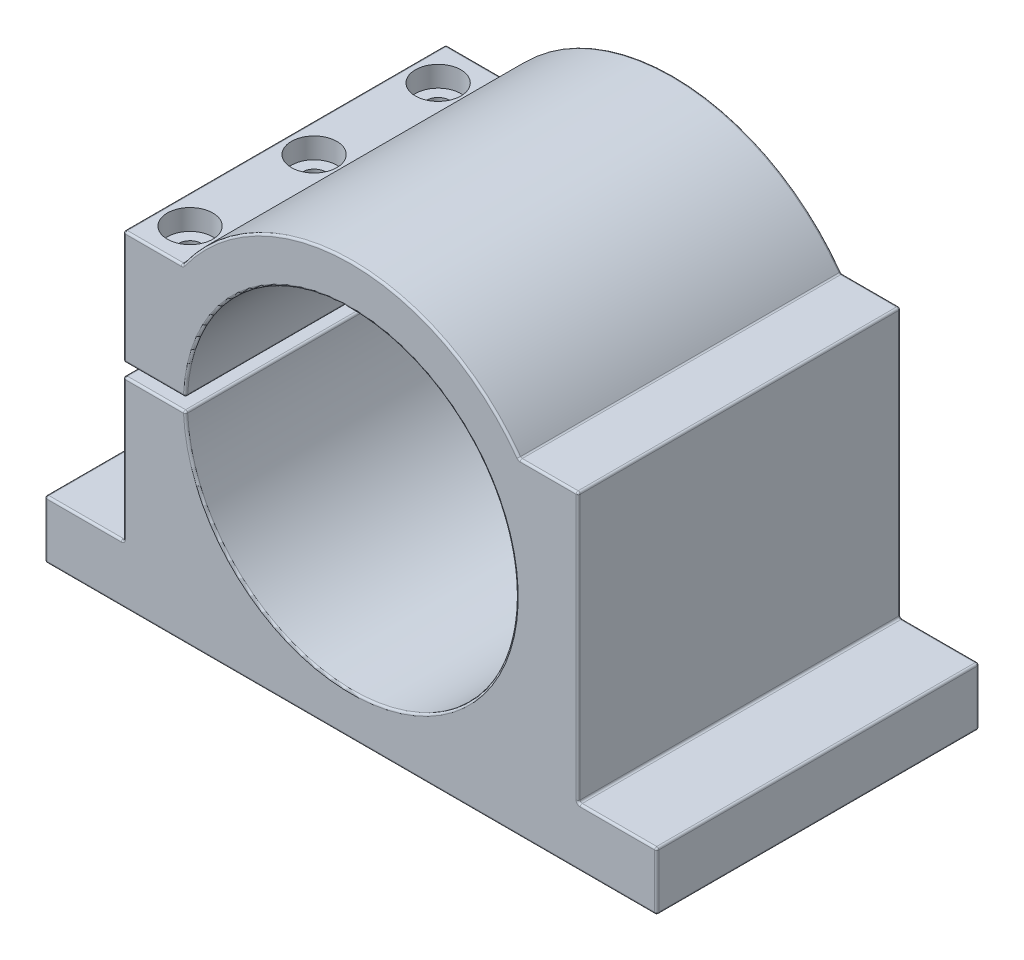
SolidWorks part; units mm, degrees
ref_plane "Спереди" through (0, 0, 0) normal (0, 0, 1) x (1, 0, 0)
ref_plane "Сверху" through (0, 0, 0) normal (0, 1, 0) x (1, 0, 0)
ref_plane "Справа" through (0, 0, 0) normal (1, 0, 0) x (0, 0, -1)
sketch "Эскиз1" plane through (0, 0, 0) normal (0, 0, 1) x (1, 0, 0)
  line L0 (0, 0) -> (0, -50) construction
  line L1 (74, -50) -> (-74, -50)
  line L2 (-74, -50) -> (-74, -36)
  line L3 (-74, -36) -> (-55, -36)
  line L4 (-55, -36) -> (-55, 29)
  line L5 (-55, 29) -> (-40.7308, 29)
  line L6 (0, 29) -> (-40.7308, 29) construction
  line L7 (-55, 1.5) -> (0, 1.5)
  line L8 (-55, 1.5) -> (-55, -1.5)
  line L9 (-55, -1.5) -> (0, -1.5)
  line L10 (0, 1.5) -> (0, -1.5)
  line L11 (0, 29) -> (0, 0) construction
  line L12 (0, -50) -> (0, 50) construction
  line L13 (55, 29) -> (40.7308, 29)
  line L14 (55, -36) -> (55, 29)
  line L15 (74, -36) -> (55, -36)
  line L16 (74, -50) -> (74, -36)
  circle A0 centre (0, 0) radius 40
  circle A2 centre (0, 0) radius 50
  point P13 (-27.55, 29)
  point P14 (0, 40)
  point P20 (0, 40)
  dimension "D1" = 80
  dimension "D2" = 3
  dimension "D3" = 50
  dimension "D4" = 14
  dimension "D5" = 148
  dimension "D6" = 19
  dimension "D7" = 65
  dimension "D8" = 10
extrude "Бобышка-Вытянуть1" add sketch "Эскиз1" along normal mid plane 78 contours A2 L1 L16 L15 L14 L13 | A2 L7 A0 L9 | A2 L9 L4 L3 L2 L1 | A2 L5 L4 L7
sketch "Эскиз2" plane through (0, 29, 0) normal (0, 1, 0) x (1, 0, 0)
  line L0 (-47.8654, 39) -> (-47.8654, -39) construction
  line L1 (-55, 39) -> (-40.7308, 39) construction
  line L2 (-55, -39) -> (-40.7308, -39) construction
  circle A0 centre (-47.8654, 30) radius 5.5
  circle A1 centre (-47.8654, 0) radius 5.5
  circle A2 centre (-47.8654, -30) radius 5.5
  dimension "D1" = 11
  dimension "D2" = 11
  dimension "D3" = 11
  dimension "D4" = 30
  dimension "D5" = 30
extrude "Вырез-Вытянуть1" cut sketch "Эскиз2" against normal blind 5
sketch "Эскиз3" plane through (0, 24, 0) normal (0, 1, 0) x (1, 0, 0)
  circle A0 centre (-47.8654, 30) radius 2.75
  circle A1 centre (-47.8654, 0) radius 2.75
  circle A2 centre (-47.8654, -30) radius 2.75
  dimension "D1" = 5.5
extrude "Вырез-Вытянуть2" cut sketch "Эскиз3" against normal up to surface (25.5 mm away) up to face at (-47.4859, -1.5, 0)
sketch "Эскиз4" plane through (0, -1.5, 0) normal (0, 1, 0) x (1, 0, 0)
  circle A0 centre (-47.8654, 30) radius 2.1
  circle A1 centre (-47.8654, 0) radius 2.1
  circle A2 centre (-47.8654, -30) radius 2.1
  dimension "D1" = 4.2
extrude "Вырез-Вытянуть3" cut sketch "Эскиз4" against normal blind 30
fillet "Скругление1" radius 0.5 42 edges at (-74, -36, 0) (74, -36, 0) (55, -36, 0) (55, 29, 0) (-55, 29, 0) (-55, 1.5, 0) (-55, -1.5, 0) (-55, -36, 0) (40.7308, 29, 0) (-40.7308, 29, 0) (-74, -50, 0) (74, -50, 0) (0, 50, -39) (-47.8654, 29, -39) (-55, 15.25, -39) (-47.4859, 1.5, -39) (-47.4859, -1.5, -39) (-55, -18.75, -39) (-64.5, -36, -39) (-74, -43, -39) (0, -50, -39) (74, -43, -39) (64.5, -36, -39) (55, -3.5, -39) (47.8654, 29, -39) (-39.9719, 1.5, 0) (-39.9719, -1.5, 0) (40, 0, -39) (55, -3.5, 39) (64.5, -36, 39) (74, -43, 39) (0, -50, 39) (-74, -43, 39) (-64.5, -36, 39) (-55, -18.75, 39) (-47.4859, -1.5, 39) (40, 0, 39) (-47.4859, 1.5, 39) (-55, 15.25, 39) (-47.8654, 29, 39) (0, 50, 39) (47.8654, 29, 39)
